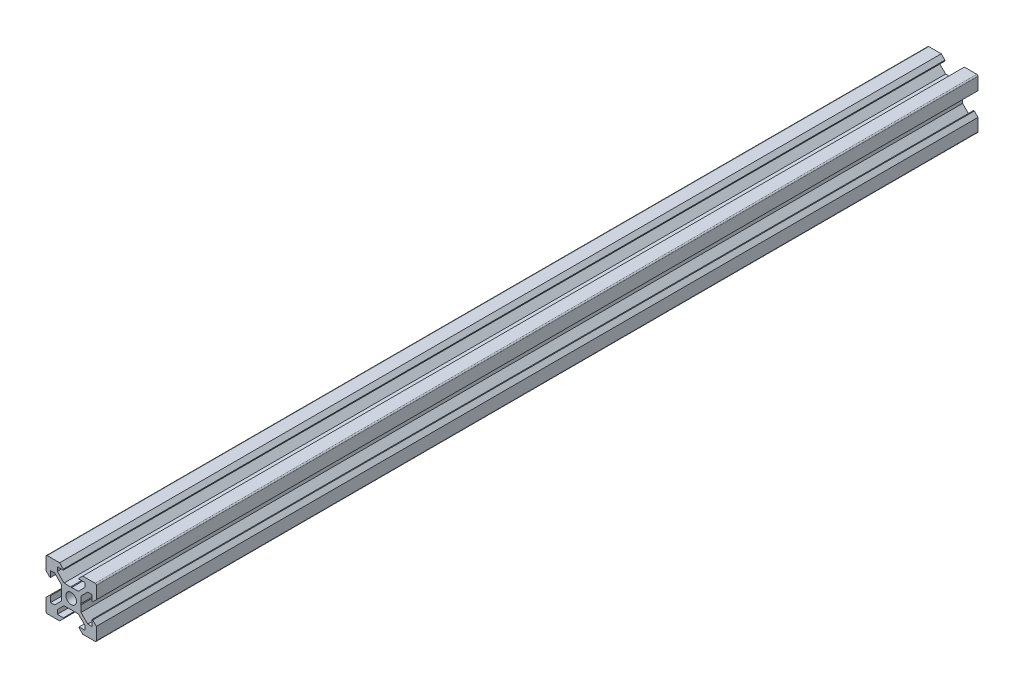
SolidWorks part; units mm, degrees
material "6061-T6 (SS)"
ref_plane "Front Plane" through (0, 0, 0) normal (0, 0, 1) x (1, 0, 0)
ref_plane "Top Plane" through (0, 0, 0) normal (0, 1, 0) x (1, 0, 0)
ref_plane "Right Plane" through (0, 0, 0) normal (1, 0, 0) x (0, 0, -1)
sketch "Sketch1" plane through (0, 0, 0) normal (0, 0, 1) x (1, 0, 0)
  line L1 (9.5, -10) -> (-9.5, -10)
  line L2 (10, -9.5) -> (10, 9.5)
  line L3 (9.5, 10) -> (-9.5, 10)
  line L4 (-10, -9.5) -> (-10, 9.5)
  line L5 (10, -10) -> (-10, 10) construction
  line L6 (10, 10) -> (-10, -10) construction
  circle A0 centre (0, 0) radius 2.1
  arc A1 (-9.5, 10) -> (-10, 9.5) centre (-9.5, 9.5) ccw
  arc A2 (10, 9.5) -> (9.5, 10) centre (9.5, 9.5) ccw
  arc A3 (9.5, -10) -> (10, -9.5) centre (9.5, -9.5) ccw
  arc A4 (-9.5, -10) -> (-10, -9.5) centre (-9.5, -9.5) cw
  point P0 (0, 0)
  line B0 (0, 0) -> (0, 10) construction
  line B1 (0, 3.69) -> (-0.21, 3.9)
  line B2 (-0.21, 3.9) -> (-2.8393, 3.9)
  line B3 (-2.8393, 3.9) -> (-5.5, 6.5607)
  line B4 (-5.5, 6.5607) -> (-5.5, 8.2)
  line B5 (-5.5, 8.2) -> (-3.125, 8.2)
  line B6 (-3.125, 8.2) -> (-3.125, 8.545)
  line B7 (-3.125, 8.545) -> (-4.58, 10)
  line B8 (-4.58, 10) -> (4.58, 10)
  line B9 (0, 0) -> (-5.9132, 5.9132) construction
  line B10 (3.125, 8.545) -> (4.58, 10)
  line B11 (3.125, 8.2) -> (3.125, 8.545)
  line B12 (5.5, 8.2) -> (3.125, 8.2)
  line B13 (5.5, 6.5607) -> (5.5, 8.2)
  line B14 (2.8393, 3.9) -> (5.5, 6.5607)
  line B15 (0.21, 3.9) -> (2.8393, 3.9)
  line B16 (0, 3.69) -> (0.21, 3.9)
  line B17 (0, 0) -> (-10, 0) construction
  line B18 (-3.69, 0) -> (-3.9, -0.21)
  line B19 (-3.9, -0.21) -> (-3.9, -2.8393)
  line B20 (-3.9, -2.8393) -> (-6.5607, -5.5)
  line B21 (-6.5607, -5.5) -> (-8.2, -5.5)
  line B22 (-8.2, -5.5) -> (-8.2, -3.125)
  line B23 (-8.2, -3.125) -> (-8.545, -3.125)
  line B24 (-8.545, -3.125) -> (-10, -4.58)
  line B25 (-10, -4.58) -> (-10, 4.58)
  line B26 (0, 0) -> (-5.9132, -5.9132) construction
  line B27 (-8.545, 3.125) -> (-10, 4.58)
  line B28 (-8.2, 3.125) -> (-8.545, 3.125)
  line B29 (-8.2, 5.5) -> (-8.2, 3.125)
  line B30 (-6.5607, 5.5) -> (-8.2, 5.5)
  line B31 (-3.9, 2.8393) -> (-6.5607, 5.5)
  line B32 (-3.9, 0.21) -> (-3.9, 2.8393)
  line B33 (-3.69, 0) -> (-3.9, 0.21)
  line B34 (0, 0) -> (0, -10) construction
  line B35 (0, -3.69) -> (0.21, -3.9)
  line B36 (0.21, -3.9) -> (2.8393, -3.9)
  line B37 (2.8393, -3.9) -> (5.5, -6.5607)
  line B38 (5.5, -6.5607) -> (5.5, -8.2)
  line B39 (5.5, -8.2) -> (3.125, -8.2)
  line B40 (3.125, -8.2) -> (3.125, -8.545)
  line B41 (3.125, -8.545) -> (4.58, -10)
  line B42 (4.58, -10) -> (-4.58, -10)
  line B43 (0, 0) -> (5.9132, -5.9132) construction
  line B44 (-3.125, -8.545) -> (-4.58, -10)
  line B45 (-3.125, -8.2) -> (-3.125, -8.545)
  line B46 (-5.5, -8.2) -> (-3.125, -8.2)
  line B47 (-5.5, -6.5607) -> (-5.5, -8.2)
  line B48 (-2.8393, -3.9) -> (-5.5, -6.5607)
  line B49 (-0.21, -3.9) -> (-2.8393, -3.9)
  line B50 (0, -3.69) -> (-0.21, -3.9)
  line B51 (0, 0) -> (10, 0) construction
  line B52 (3.69, 0) -> (3.9, 0.21)
  line B53 (3.9, 0.21) -> (3.9, 2.8393)
  line B54 (3.9, 2.8393) -> (6.5607, 5.5)
  line B55 (6.5607, 5.5) -> (8.2, 5.5)
  line B56 (8.2, 5.5) -> (8.2, 3.125)
  line B57 (8.2, 3.125) -> (8.545, 3.125)
  line B58 (8.545, 3.125) -> (10, 4.58)
  line B59 (10, 4.58) -> (10, -4.58)
  line B60 (0, 0) -> (5.9132, 5.9132) construction
  line B61 (8.545, -3.125) -> (10, -4.58)
  line B62 (8.2, -3.125) -> (8.545, -3.125)
  line B63 (8.2, -5.5) -> (8.2, -3.125)
  line B64 (6.5607, -5.5) -> (8.2, -5.5)
  line B65 (3.9, -2.8393) -> (6.5607, -5.5)
  line B66 (3.9, -0.21) -> (3.9, -2.8393)
  line B67 (3.69, 0) -> (3.9, -0.21)
  dimension "D1" = 4.2
  dimension "D3" = 0.5
  dimension "D2" = 20
sketch_block_instance "V Slot 1-4"
sketch_block "V Slot 1" parameters "D1"=10, "D2"=11, "D3"=4.3, "D4"=1.8, "D5"=0.21, "D6"=45, "D7"=9.16, "D8"=1.5, "D9"=6.25
sketch_block_instance "V Slot 1-5"
sketch_block_instance "V Slot 1-6"
sketch_block_instance "V Slot 1-7"
extrude "Boss-Extrude1" add sketch "Sketch1" along normal blind 350 contours B67 B52 B53 B54 B55 B56 B57 B58 L2 A2 L3 B10 B11 B12 B13 B14 B15 B16 B1 B2 B3 B4 B5 B6 B7 A1 L4 B27 B28 B29 B30 B31 B32 B33 B18 B19 B20 B21 B22 B23 B24 A4 L1 B44 B45 B46 B47 B48 B49
